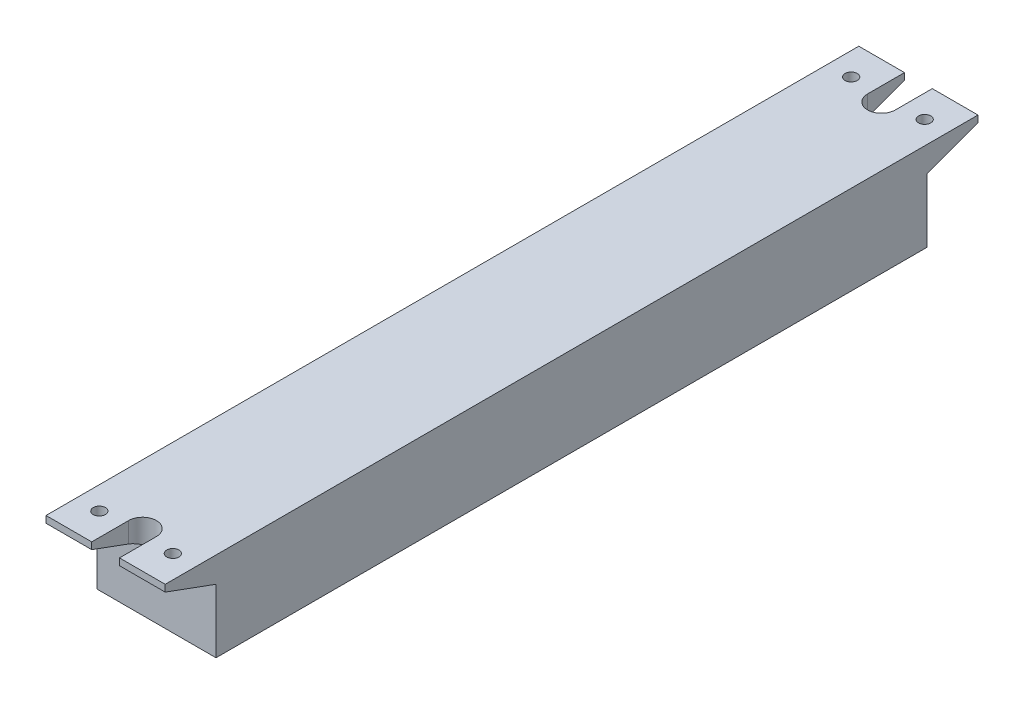
SolidWorks part; units mm, degrees
ref_plane "Plano frontal" through (0, 0, 0) normal (0, 0, 1) x (1, 0, 0)
ref_plane "Plano superior" through (0, 0, 0) normal (0, 1, 0) x (1, 0, 0)
ref_plane "Plano direito" through (0, 0, 0) normal (1, 0, 0) x (0, 0, -1)
sketch "Esboço1" plane through (0, 0, 0) normal (1, 0, 0) x (0, 0, -1)
  line L0 (-105, 13.15) -> (-120, 13.15)
  line L1 (105, -13.15) -> (-105, -13.15)
  line L2 (105, -13.15) -> (105, 5.65)
  line L3 (105, 13.15) -> (-105, 13.15)
  line L4 (-105, -13.15) -> (-105, 5.65)
  line L5 (105, -13.15) -> (-105, 13.15) construction
  line L6 (105, 13.15) -> (-105, -13.15) construction
  line L7 (-120, 13.15) -> (-120, 11.15)
  line L8 (-120, 11.15) -> (-105, 5.65)
  line L9 (0, 32.2314) -> (0, -33.9461) construction
  line L10 (120, 11.15) -> (105, 5.65)
  line L11 (120, 13.15) -> (120, 11.15)
  line L12 (105, 13.15) -> (120, 13.15)
  point P0 (0, 0)
  dimension "D1" = 26.3
  dimension "D2" = 210
  dimension "D3" = 15
  dimension "D4" = 2
  dimension "D5" = 7.5
extrude "Ressalto-extrusão1" add sketch "Esboço1" along normal blind 35.2
sketch "Esboço2" plane through (0, -13.15, 0) normal (0, -1, 0) x (1, 0, 0)
  line L0 (17.6, 140.3643) -> (17.6, -142.254) construction
  line L1 (-24.2488, 0) -> (76.0807, 0) construction
  line L2 (35.2, 105) -> (0, 105) construction
  line L3 (13.5, 109.1) -> (13.5, 120)
  line L4 (35.2, 120) -> (0, 120) construction
  line L5 (21.7, 109.1) -> (21.7, 120)
  line L6 (13.5, 120) -> (21.7, 120)
  line L7 (13.5, -120) -> (21.7, -120)
  line L8 (21.7, -109.1) -> (21.7, -120)
  line L9 (13.5, -109.1) -> (13.5, -120)
  line L10 (35.2, 105) -> (0, 105) construction
  line L11 (0, 120) -> (0, 105) construction
  arc A0 (13.5, 109.1) -> (21.7, 109.1) centre (17.6, 109.1) ccw
  arc A1 (13.5, -109.1) -> (21.7, -109.1) centre (17.6, -109.1) cw
  circle A2 centre (6.75, 111) radius 1.8
  circle A3 centre (28.45, 111) radius 1.8
  circle A4 centre (28.45, -111) radius 1.8
  circle A5 centre (6.75, -111) radius 1.8
  dimension "D1" = 8.2
  dimension "D2" = 3.6
  dimension "D3" = 6
  dimension "D4" = 6.75
extrude "Corte-extrusão1" cut sketch "Esboço2" against normal blind 35.2
